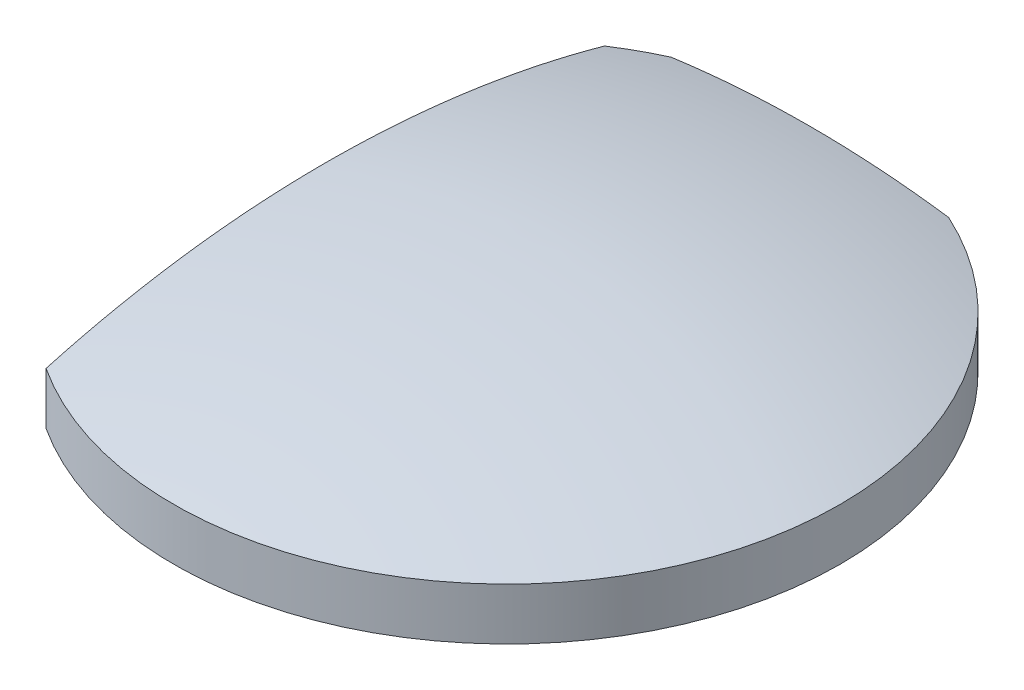
SolidWorks part; units mm, degrees
material "Стекло"
ref_plane "Спереди" through (0, 0, 0) normal (0, 0, 1) x (1, 0, 0)
ref_plane "Сверху" through (0, 0, 0) normal (0, 1, 0) x (1, 0, 0)
ref_plane "Справа" through (0, 0, 0) normal (1, 0, 0) x (0, 0, -1)
sketch "Эскиз1" plane through (0, 0, 0) normal (1, 0, 0) x (0, 0, -1)
  line L0 (0, 3.5) -> (11, 3.5) construction
  line L1 (0, 0) -> (11, 0)
  line L2 (11, 0) -> (11, 1.713)
  line L3 (0, 3.5) -> (0, 0)
  arc A0 (11, 1.713) -> (0, 3.5) centre (0, -31.25) ccw
  dimension "D1" = 34.75
  dimension "D2" = 3.5
  dimension "D3" = 11
revolve "Повернуть1" add sketch "Эскиз1" angle 360 about L3
sketch "Эскиз2" plane through (0, 0, 0) normal (0, -1, 0) x (1, 0, 0)
  line L0 (-6, -10) -> (-6, 9.2195)
  line L1 (-6, -10) -> (4.5826, -10)
  circle A0 centre (0, 0) radius 11 construction
  circle M5 centre (0, 0) radius 11
  dimension "D1" = 10
  dimension "D2" = 6
extrude "Вырез-Вытянуть1" cut sketch "Эскиз2" against normal through all contours L0 M5 | L1 M5
